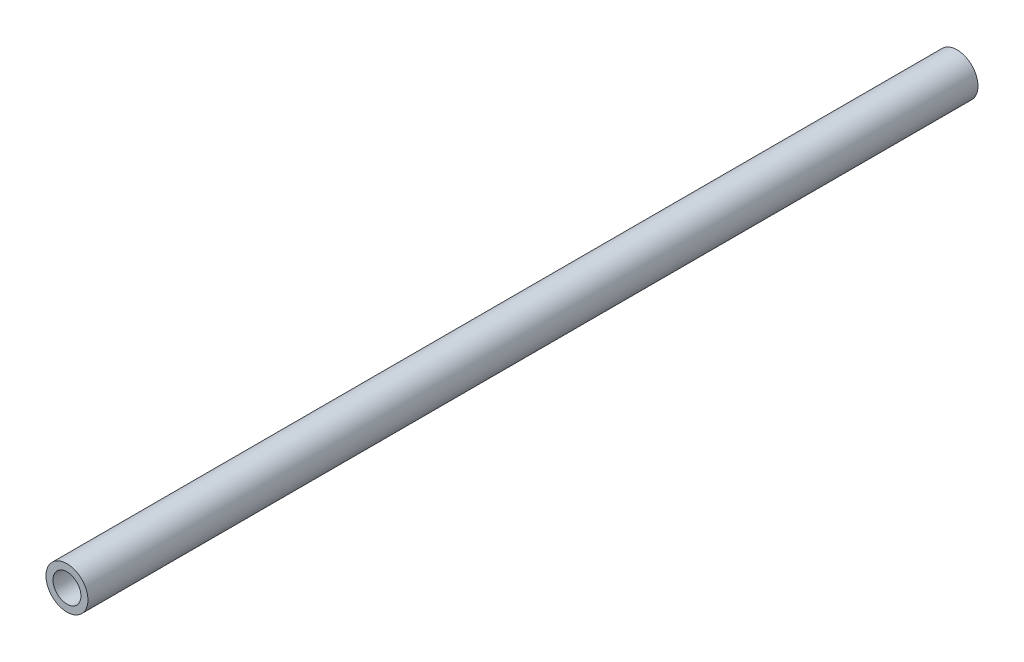
SolidWorks part; units mm, degrees
ref_plane "Front Plane" through (0, 0, 0) normal (0, 0, 1) x (1, 0, 0)
ref_plane "Top Plane" through (0, 0, 0) normal (0, 1, 0) x (1, 0, 0)
ref_plane "Right Plane" through (0, 0, 0) normal (1, 0, 0) x (0, 0, -1)
sketch "Sketch1" plane through (0, 0, 0) normal (0, 0, 1) x (1, 0, 0)
  circle A0 centre (0, 0) radius 2
  circle A1 centre (0, 0) radius 3
  dimension "D1" = 4
  dimension "D2" = 1
extrude "Boss-Extrude1" add sketch "Sketch1" along normal blind 127.28
